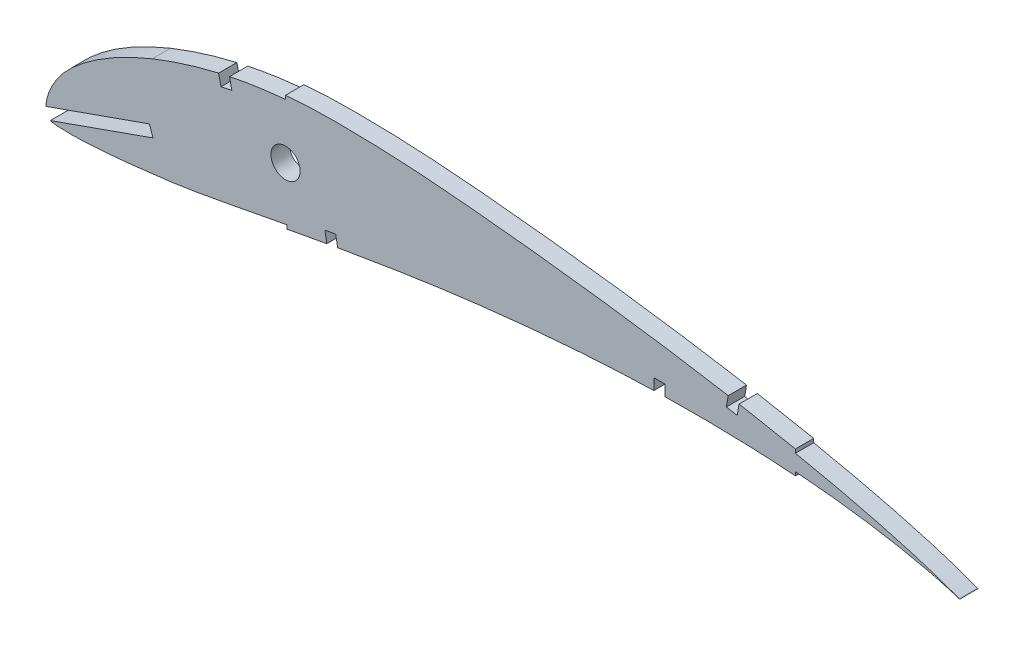
SolidWorks part; units mm, degrees
material "Balsa"
ref_plane "Front Plane" through (0, 0, 0) normal (0, 0, 1) x (1, 0, 0)
ref_plane "Top Plane" through (0, 0, 0) normal (0, 1, 0) x (1, 0, 0)
ref_plane "Right Plane" through (0, 0, 0) normal (1, 0, 0) x (0, 0, -1)
sketch "Sketch1" plane through (0, 0, 0) normal (0, 0, 1) x (1, 0, 0)
  line L0 (-185.5394, 13.946) -> (80.4606, 13.946) construction
  line L1 (80.4606, 13.946) -> (20.4606, 13.946) construction
  line L2 (20.4606, 28.9183) -> (20.4606, 29.9281)
  line L3 (-185.5394, 13.946) -> (-119.0394, 13.946) construction
  line L4 (-119.0394, 49.3628) -> (-119.0394, 48.3677)
  line L5 (-118.708, 18.8467) -> (-118.708, 17.8168)
  line L6 (-119.0394, 48.3677) -> (-119.0394, 67.3466) construction
  line L7 (-119.0394, 19.2581) -> (-119.0394, 47.6489) construction
  line L8 (20.4606, 34.2821) -> (20.4606, 35.3026)
  line L9 (-134.3619, 46.1126) -> (-133.7515, 43.1753)
  line L10 (-133.7515, 43.1753) -> (-136.6887, 42.5649)
  line L11 (71.9997, 18.6516) -> (71.9997, 18.6465)
  line L12 (67.6399, 20.3742) -> (67.6399, 20.3688)
  line L13 (-136.6887, 42.5649) -> (-137.3607, 45.452)
  line L14 (67.3547, 20.4754) -> (67.3547, 20.4699)
  line L15 (-107.7411, 19.8325) -> (-108.2697, 22.7856)
  line L16 (-108.2697, 22.7856) -> (-105.3166, 23.3142)
  line L17 (-105.3166, 23.3142) -> (-104.7961, 20.3552)
  line L18 (2.0834, 38.7561) -> (1.5706, 35.8003)
  line L19 (1.5706, 35.8003) -> (4.5265, 35.2875)
  line L20 (4.5265, 35.2875) -> (5.0505, 38.2351)
  line L21 (-184.5797, 13.946) -> (-156.295, 23.9447)
  line L22 (-156.295, 23.9447) -> (-155.2951, 21.1163)
  line L23 (-155.2951, 21.1163) -> (-183.3946, 11.183)
  line L24 (-15.2749, 29.8336) -> (-15.2749, 32.8336)
  line L25 (-15.2749, 32.8336) -> (-18.2749, 32.8336)
  line L26 (-18.2749, 32.8336) -> (-18.2749, 29.7643)
  line L27 (65.169, 22.2616) -> (65.3099, 22.2168)
  line L28 (65.3099, 22.2168) -> (65.3703, 22.1976)
  line L29 (65.2751, 22.24) -> (65.415, 22.1855)
  line L30 (65.3703, 22.1976) -> (65.415, 22.1855)
  circle A0 centre (-119.0394, 33.3312) radius 4
  spline S0 degree 3 poles (-182.6337, 9.9642) (-182.6336, 9.9642) (-182.6336, 9.9642) (-182.6336, 9.9642) knots 0.520818 0.520818 0.520818 0.520818 0.520819 0.520819 0.520819 0.520819
  spline S1 degree 3 poles (-118.708, 17.8168) (-116.4493, 18.2408) (-112.795, 18.9202) (-109.1377, 19.5826) (-107.7411, 19.8325) knots 0.636684 0.636684 0.636684 0.636684 0.649056 0.656694 0.656694 0.656694 0.656694
  spline S2 degree 3 poles (-182.6337, 9.9642) (-182.6336, 9.9642) (-182.6335, 9.9642) (-182.6334, 9.9642) knots 0.520883 0.520883 0.520883 0.520883 0.520883 0.520883 0.520883 0.520883 construction
  spline S3 degree 3 poles (2.0834, 38.7561) (-0.7289, 39.244) (-6.6963, 40.2438) (-15.8979, 41.669) (-25.5589, 43.0566) (-35.3611, 44.3558) (-45.2335, 45.5625) (-55.0973, 46.6852) (-64.8708, 47.6956) (-74.4743, 48.5749) (-83.8403, 49.2734) (-92.9153, 49.7539) (-101.6488, 49.9614) (-109.9961, 49.9393) (-115.7492, 49.6434) (-118.7115, 49.3918) (-119.0394, 49.3628) knots 1.149184 1.149184 1.149184 1.149184 1.164551 1.181758 1.199312 1.217095 1.23499 1.252857 1.270541 1.287887 1.304773 1.321101 1.336806 1.3518 1.366031 1.367803 1.367803 1.367803 1.367803
  spline S4 degree 3 poles (-119.0394, 48.3677) (-122.1014, 48.0952) (-127.235, 47.4662) (-132.3152, 46.5379) (-134.3619, 46.1126) knots 0.367899 0.367899 0.367899 0.367899 0.384571 0.395914 0.395914 0.395914 0.395914
  spline S5 degree 3 poles (20.4606, 35.3026) (20.3944, 35.3161) (17.4924, 35.9064) (12.3605, 36.9104) (7.283, 37.8383) (5.0505, 38.2351) knots 1.115627 1.115627 1.115627 1.115627 1.115991 1.13157 1.143778 1.143778 1.143778 1.143778
  spline S6 degree 3 poles (-66.2524, 26.1361) (-65.9915, 26.1675) (-61.55, 26.6996) (-52.8747, 27.6428) (-40.2023, 28.7189) (-28.6514, 29.4128) (-21.338, 29.683) (-18.2749, 29.7643) knots 0.732012 0.732012 0.732012 0.732012 0.733427 0.756094 0.778989 0.80189 0.818385 0.818385 0.818385 0.818385
  spline S7 degree 3 poles (-155.5158, 39.7592) (-158.1988, 38.6749) (-163.6477, 36.2112) (-170.1461, 32.4494) (-175.0894, 28.8172) (-178.5241, 25.8006) (-180.9547, 22.934) (-182.5624, 20.399) (-183.5594, 18.4102) (-184.1652, 16.6769) (-184.4771, 15.2621) (-184.5655, 14.4723) (-184.5786, 14.0384) (-184.5797, 13.946) knots 0.435917 0.435917 0.435917 0.435917 0.451639 0.468407 0.47679 0.485174 0.493557 0.497749 0.501941 0.506133 0.508229 0.510325 0.510894 0.510894 0.510894 0.510894
  spline S8 degree 3 poles (-183.3946, 11.183) (-183.2696, 11.1366) (-182.9793, 11.0474) (-182.3571, 10.9179) (-181.481, 10.8445) (-180.3109, 10.8005) (-178.7734, 10.7442) (-176.8638, 10.726) (-174.5623, 10.8058) (-172.2397, 10.9322) (-169.147, 11.1314) (-165.2845, 11.4479) (-160.6499, 11.9107) (-156.02, 12.4347) (-151.3971, 13.0129) (-145.26, 13.893) (-137.6166, 15.2364) (-128.2603, 17.0426) (-121.9537, 18.2374) (-118.708, 18.8467) knots 0.518864 0.518864 0.518864 0.518864 0.519756 0.520804 0.5229 0.524996 0.527092 0.531284 0.535475 0.539667 0.543859 0.552243 0.560626 0.56901 0.577393 0.585777 0.602544 0.619311 0.637085 0.637085 0.637085 0.637085
  spline S9 degree 3 poles (80.4592, 13.946) (80.46, 13.9457) (80.4617, 13.9457) (80.4583, 13.9492) (80.4536, 13.9534) knots 0.99996 0.99996 0.99996 0.99996 1 1.000102 1.000102 1.000102 1.000102
  spline S10 degree 3 poles (20.4606, 29.9281) (24.2721, 29.6385) (31.8289, 28.9241) (43.0938, 27.389) (54.2186, 25.2847) (61.5648, 23.4077) (65.169, 22.2616) knots 0.887815 0.887815 0.887815 0.887815 0.908324 0.928538 0.948751 0.968965 0.968965 0.968965 0.968965
  spline S11 degree 3 poles (65.2751, 22.24) (61.6794, 23.641) (54.3534, 26.0668) (43.15, 29.165) (31.8901, 31.8734) (24.3316, 33.4925) (20.5313, 34.2677) (20.4871, 34.2767) (20.4606, 34.2821) knots 1.031789 1.031789 1.031789 1.031789 1.052706 1.073623 1.094539 1.115213 1.11531 1.115456 1.115456 1.115456 1.115456
  spline S12 degree 3 poles (-137.3607, 45.452) (-140.3476, 44.7568) (-146.2971, 43.1459) (-152.2942, 41.0515) (-155.3374, 39.8312) (-155.5158, 39.7592) knots 0.401467 0.401467 0.401467 0.401467 0.418105 0.434872 0.435917 0.435917 0.435917 0.435917
  spline S13 degree 3 poles (-104.7961, 20.3552) (-103.5593, 20.5727) (-98.5207, 21.4488) (-89.5164, 22.9327) (-77.9059, 24.6575) (-70.0924, 25.6735) (-66.2524, 26.1361) knots 0.662062 0.662062 0.662062 0.662062 0.668822 0.689595 0.71119 0.732012 0.732012 0.732012 0.732012
  spline S14 degree 3 poles (-15.2749, 29.8336) (-15.127, 29.8365) (-10.8514, 29.9185) (-2.5719, 29.954) (9.1977, 29.6421) (16.8296, 29.195) (20.4606, 28.9183) knots 0.82377 0.82377 0.82377 0.82377 0.824567 0.846792 0.868338 0.887942 0.887942 0.887942 0.887942
extrude "Boss-Extrude2" add sketch "Sketch1" along normal blind 5 contours L24 S14 L2 S10 L27 L28 L30 L29 S11 L8 S5 L20 L19 L18 S3 L4 S4 L9 L10 L13 S12 S7 L21 L22 L23 S8 L5 S1 L15 L16 L17 S13 S6 L26 L25 A0
